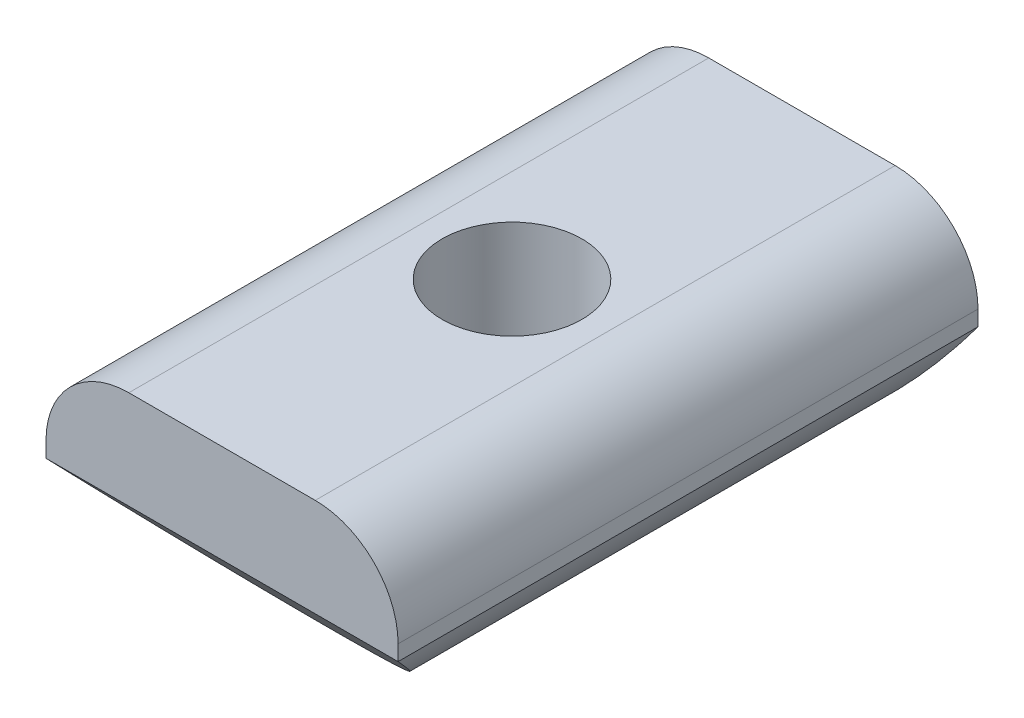
SolidWorks part; units mm, degrees
ref_plane "Plan de face" through (0, 0, 0) normal (0, 0, 1) x (1, 0, 0)
ref_plane "Plan de dessus" through (0, 0, 0) normal (0, 1, 0) x (1, 0, 0)
ref_plane "Plan de droite" through (0, 0, 0) normal (1, 0, 0) x (0, 0, -1)
sketch "Esquisse1" plane through (0, 0, 0) normal (0, 0, 1) x (1, 0, 0)
  line L0 (0, 0) -> (0, -13.1926) construction
  line L2 (-8.5, -4.2426) -> (-8.5, -3.5)
  line L3 (-4.5, 0.5) -> (4.5, 0.5)
  line L4 (8.5, -4.2426) -> (8.5, -3.5)
  arc A0 (-8.5, -4.2426) -> (8.5, -4.2426) centre (0, 0) ccw
  arc A1 (-4.5, 0.5) -> (-8.5, -3.5) centre (-4.5, -3.5) ccw
  arc A2 (4.5, 0.5) -> (8.5, -3.5) centre (4.5, -3.5) cw
  dimension "D1" = 19
  dimension "D2" = 10
  dimension "D4" = 4
  dimension "D3" = 17
extrude "Extrusion1" add sketch "Esquisse1" along normal mid plane 28
sketch "Esquisse2" plane through (0, 0.5, 0) normal (0, 1, 0) x (-1, 0, 0)
  circle A0 centre (0, 0) radius 3.375
  dimension "D1" = 6.75
extrude "Enlèv. mat.-Extru.1" cut sketch "Esquisse2" against normal through all
sketch "Esquisse3" plane through (0, 0, 0) normal (1, 0, 0) x (0, 0, -1)
  line L0 (14, -9.5) -> (14, -4.2426)
  line L1 (14, -9.5) -> (14, -4.2426) construction
  line L2 (14, -4.2426) -> (9, -9.5)
  line L3 (9, -9.5) -> (14, -9.5)
  line L4 (0, 0) -> (0, -14.0186) construction
  line L5 (-14, -9.5) -> (-14, -4.2426)
  line L6 (-9, -9.5) -> (-14, -9.5)
  line L7 (-14, -4.2426) -> (-9, -9.5)
  line L8 (-14, -4.2426) -> (14, -4.2426) construction
  dimension "D1" = 18
extrude "Enlèv. mat.-Extru.2" cut sketch "Esquisse3" against normal through all and the other way through all
